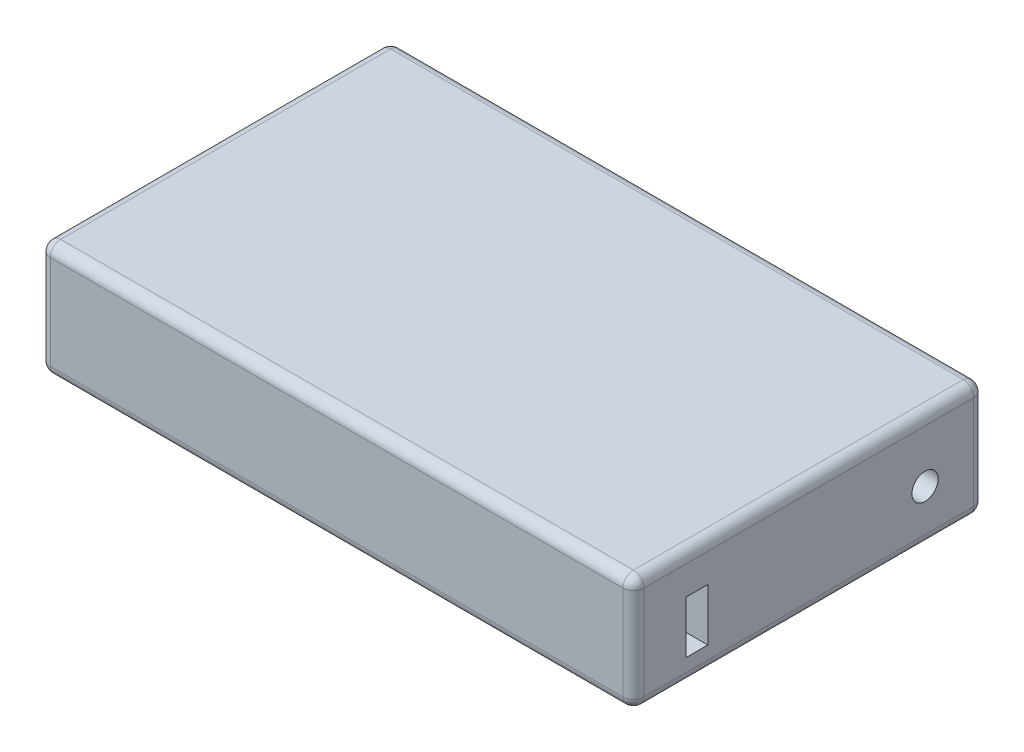
SolidWorks part; units mm, degrees
material "Battery Pack mat'l"
ref_plane "Front Plane" through (0, 0, 0) normal (0, 0, 1) x (1, 0, 0)
ref_plane "Top Plane" through (0, 0, 0) normal (0, 1, 0) x (1, 0, 0)
ref_plane "Right Plane" through (0, 0, 0) normal (1, 0, 0) x (0, 0, -1)
sketch "Sketch1" plane through (0, 0, 0) normal (0, 1, 0) x (1, 0, 0)
  line L1 (-72.009, 42.545) -> (72.009, 42.545)
  line L2 (-72.009, 42.545) -> (-72.009, -42.545)
  line L3 (-72.009, -42.545) -> (72.009, -42.545)
  line L4 (72.009, 42.545) -> (72.009, -42.545)
  line L5 (-72.009, 42.545) -> (72.009, -42.545) construction
  line L6 (-72.009, -42.545) -> (72.009, 42.545) construction
  point P0 (0, 0)
  dimension "D1" = 144.018
  dimension "D2" = 85.09
extrude "Boss-Extrude1" add sketch "Sketch1" along normal blind 27.94
fillet "Fillet1" radius 2.54 12 edges at (-72.009, 13.97, -42.545) (0, 0, -42.545) (-72.009, 0, 0) (72.009, 13.97, -42.545) (72.009, 0, 0) (-72.009, 13.97, 42.545) (72.009, 13.97, 42.545) (0, 0, 42.545) (0, 27.94, 42.545) (-72.009, 27.94, 0) (0, 27.94, -42.545) (72.009, 27.94, 0)
sketch "Sketch3" plane through (72.009, 0, 0) normal (1, 0, 0) x (0, 0, -1)
  line L0 (-42.545, 27.94) -> (-42.545, 0) construction
  line L1 (-29.845, 18.415) -> (-24.511, 18.415)
  line L2 (-29.845, 18.415) -> (-29.845, 5.715)
  line L3 (-29.845, 5.715) -> (-24.511, 5.715)
  line L4 (-24.511, 18.415) -> (-24.511, 5.715)
  line L5 (-42.545, 0) -> (42.545, 0) construction
  line L6 (42.545, 27.94) -> (42.545, 0) construction
  circle A0 centre (28.194, 12.7) radius 3.175
  dimension "D5" = 6.35
  dimension "D1" = 5.334
  dimension "D2" = 12.7
  dimension "D3" = 12.7
  dimension "D4" = 5.715
  dimension "D6" = 14.351
  dimension "D7" = 12.7
extrude "Cut-Extrude1" cut sketch "Sketch3" against normal blind 12.7
